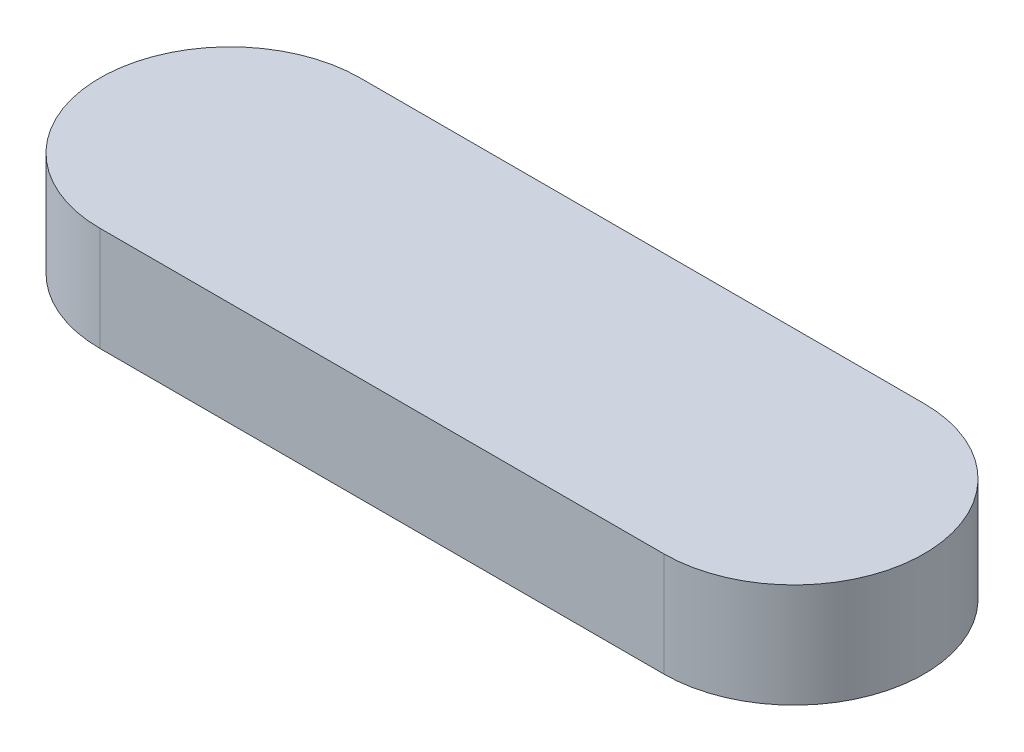
SolidWorks part; units mm, degrees
ref_plane "Front Plane" through (0, 0, 0) normal (0, 0, 1) x (1, 0, 0)
ref_plane "Top Plane" through (0, 0, 0) normal (0, 1, 0) x (1, 0, 0)
ref_plane "Right Plane" through (0, 0, 0) normal (1, 0, 0) x (0, 0, -1)
sketch "Sketch1" plane through (0, 0, 0) normal (0, 1, 0) x (1, 0, 0)
  line L0 (-32.5, 0) -> (32.5, 0) construction
  line L1 (-32.5, 15) -> (32.5, 15)
  line L2 (-32.5, -15) -> (32.5, -15)
  arc A0 (-32.5, 15) -> (-32.5, -15) centre (-32.5, 0) ccw
  arc A1 (32.5, -15) -> (32.5, 15) centre (32.5, 0) ccw
  point P3 (0, 0)
  point P8 (0, 0)
  dimension "D1" = 30
  dimension "D2" = 65
extrude "Boss-Extrude1" add sketch "Sketch1" along normal blind 12 contours A0 L2 A1 L1
